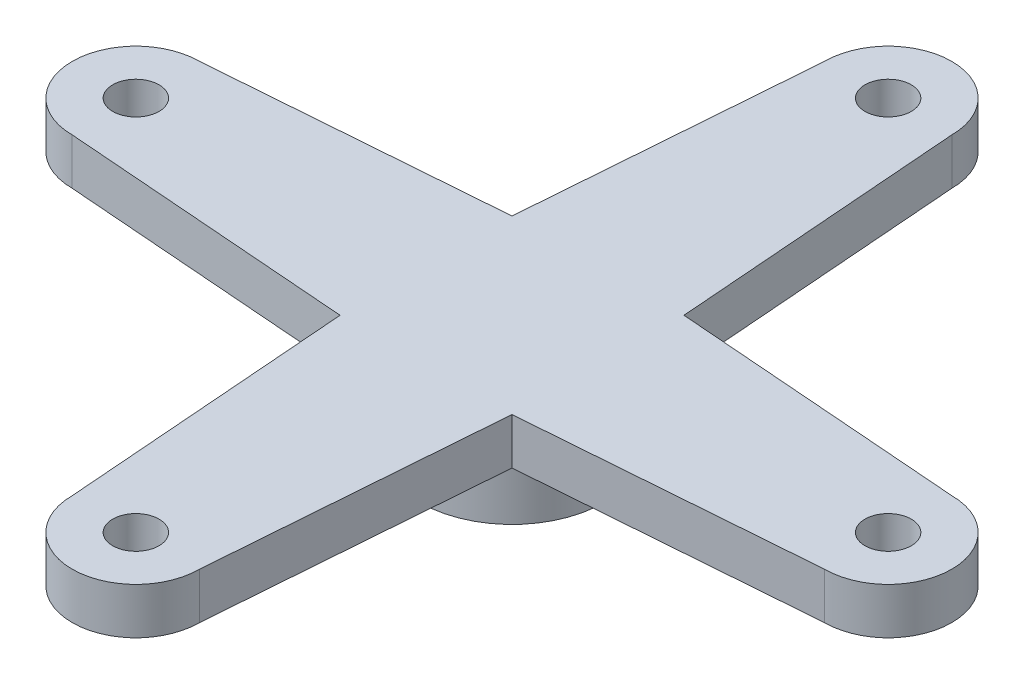
SolidWorks part; units mm, degrees
ref_plane "Front Plane" through (0, 0, 0) normal (0, 0, 1) x (1, 0, 0)
ref_plane "Top Plane" through (0, 0, 0) normal (0, 1, 0) x (1, 0, 0)
ref_plane "Right Plane" through (0, 0, 0) normal (1, 0, 0) x (0, 0, -1)
sketch "Sketch1" plane through (0, 0, 0) normal (0, 1, 0) x (1, 0, 0)
  circle A0 centre (0, 0) radius 4
  dimension "D1" = 8
extrude "Boss-Extrude1" add sketch "Sketch1" along normal blind 3
sketch "Sketch2" plane through (0, 3, 0) normal (0, 1, 0) x (1, 0, 0)
  line L0 (0, 0) -> (19, 0) construction
  line L1 (3.7143, 3.7143) -> (16.25, 2.75)
  line L2 (3.7143, -3.7143) -> (16.25, -2.75)
  line L3 (3.7143, -3.7143) -> (2.75, -16.25)
  line L4 (-3.7143, -3.7143) -> (-2.75, -16.25)
  line L5 (0, 0) -> (0, -19) construction
  line L6 (-3.7143, -3.7143) -> (-16.25, -2.75)
  line L7 (-3.7143, 3.7143) -> (-16.25, 2.75)
  line L8 (0, 0) -> (-19, 0) construction
  line L9 (-3.7143, 3.7143) -> (-2.75, 16.25)
  line L10 (3.7143, 3.7143) -> (2.75, 16.25)
  line L11 (0, 0) -> (0, 19) construction
  circle A0 centre (16.25, 0) radius 1
  circle A1 centre (16.25, 0) radius 2.75
  circle A3 centre (0, -16.25) radius 2.75
  circle A4 centre (0, -16.25) radius 1
  circle A5 centre (-16.25, 0) radius 2.75
  circle A6 centre (-16.25, 0) radius 1
  circle A7 centre (0, 16.25) radius 2.75
  circle A8 centre (0, 16.25) radius 1
  point P3 (16.25, 0)
  circle M4 centre (0, 0) radius 4
  dimension "D3" = 2
  dimension "D1" = 19
  dimension "D2" = 16.25
  dimension "D4" = 4
extrude "Boss-Extrude3" add sketch "Sketch2" along normal blind 2 separate body contours A7 L9 L7 A5 L6 L4 A3 L3 L2 A1 L1 L10 M4 | A5 A6 | A7 A8 | A1 A0 | A3 A4 | M4
